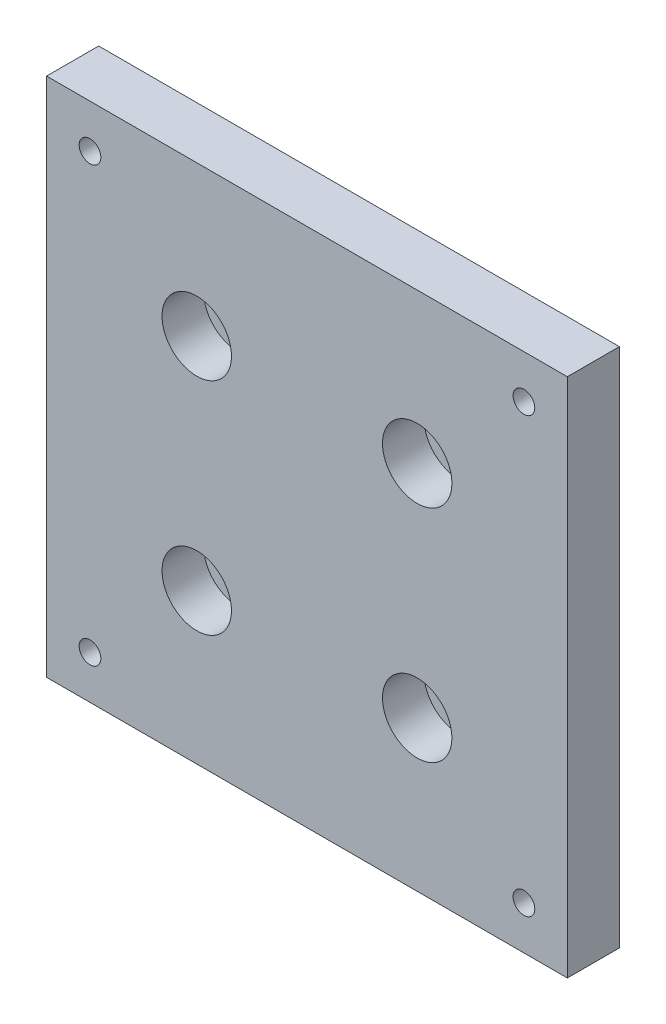
SolidWorks part; units mm, degrees
ref_plane "前视基准面" through (0, 0, 0) normal (0, 0, 1) x (1, 0, 0)
ref_plane "上视基准面" through (0, 0, 0) normal (0, 1, 0) x (1, 0, 0)
ref_plane "右视基准面" through (0, 0, 0) normal (1, 0, 0) x (0, 0, -1)
sketch "草图1" plane through (0, 0, 0) normal (0, 0, 1) x (1, 0, 0)
  line L1 (-30, 30) -> (30, 30)
  line L2 (-30, 30) -> (-30, -30)
  line L3 (-30, -30) -> (30, -30)
  line L4 (30, 30) -> (30, -30)
  line L5 (-30, 30) -> (30, -30) construction
  line L6 (-30, -30) -> (30, 30) construction
  point P0 (0, 0)
  dimension "D1" = 60
extrude "凸台-拉伸1" add sketch "草图1" along normal blind 6
sketch "草图2" plane through (0, 0, 6) normal (0, 0, 1) x (1, 0, 0)
  line L1 (25, -25) -> (-25, -25) construction
  line L2 (25, -25) -> (25, 25) construction
  line L3 (25, 25) -> (-25, 25) construction
  line L4 (-25, -25) -> (-25, 25) construction
  line L5 (25, -25) -> (-25, 25) construction
  line L6 (25, 25) -> (-25, -25) construction
  line L7 (12.7, -12.7) -> (-12.7, -12.7) construction
  line L8 (12.7, -12.7) -> (12.7, 12.7) construction
  line L9 (12.7, 12.7) -> (-12.7, 12.7) construction
  line L10 (-12.7, -12.7) -> (-12.7, 12.7) construction
  line L11 (12.7, -12.7) -> (-12.7, 12.7) construction
  line L12 (12.7, 12.7) -> (-12.7, -12.7) construction
  point P0 (0, 0)
  point P6 (0, 0)
  dimension "D1" = 25.4
  dimension "D2" = 50
hole_wizard "M3 螺纹孔1" positions "3D草图1" profile "草图3" tap size "M3" standard "ISO" end condition through all
sketch3d "3D草图1"
  point P0 (-25, 25, 6)
  point P3 (25, 25, 6)
  point P6 (25, -25, 6)
  point P9 (-25, -25, 6)
sketch "草图3" plane through (-25, 25, 6) normal (1, 0, 0) x (0, -1, 0)
  line L0 (0, 0) -> (0, 6)
  line L1 (0, 6) -> (1.25, 6)
  line L2 (1.25, 6) -> (1.25, 0)
  line L5 (1.25, 0) -> (0, 0)
  line L11 (0, -6.35) -> (0, 107.95) construction
  dimension "通孔螺纹孔钻头直径" = 2.5
  dimension "通孔螺纹孔钻头深度" = 6
cosmetic thread "孔螺蚊线1" parameters "D2"=3
cosmetic thread "孔螺蚊线2" parameters "D2"=3
cosmetic thread "孔螺蚊线3" parameters "D2"=3
cosmetic thread "孔螺蚊线4" parameters "D2"=3
hole_wizard "孔1" positions "3D草图2" profile "草图4" legacy end condition through all
sketch3d "3D草图2"
  point P0 (-12.7, 12.7, 6)
  point P3 (12.7, 12.7, 6)
  point P6 (12.7, -12.7, 6)
  point P9 (-12.7, -12.7, 6)
sketch "草图4" plane through (-12.7, 12.7, 6) normal (1, 0, 0) x (0, -1, 0)
  line L0 (0, 0) -> (0, 6)
  line L1 (0, 6) -> (2, 6)
  line L2 (2, 6) -> (2, 4.8)
  line L3 (2, 4.8) -> (4, 4.8)
  line L4 (4, 4.8) -> (4, 0)
  line L5 (4, 0) -> (0, 0)
  line L6 (0, 110) -> (0, -10) construction
  dimension "直径" = 4
  dimension "深度" = 6
  dimension "柱坑直径" = 8
  dimension "柱坑深度" = 4.8
